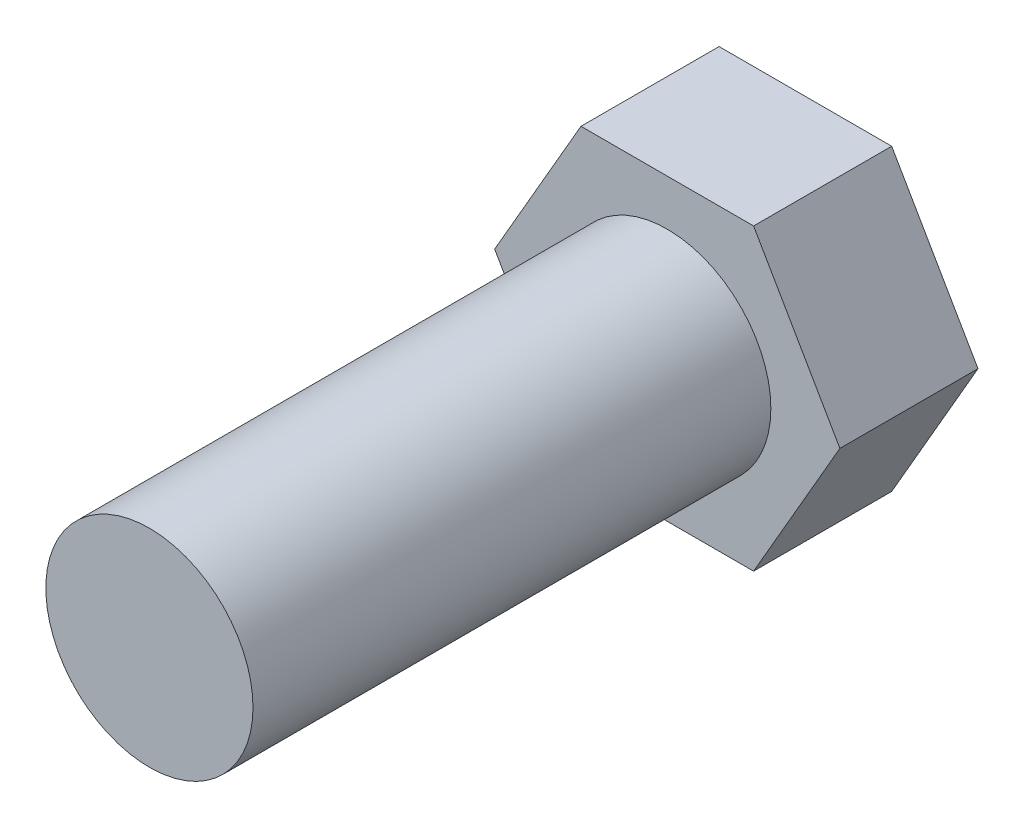
SolidWorks part; units mm, degrees
ref_plane "Alzado" through (0, 0, 0) normal (0, 0, 1) x (1, 0, 0)
ref_plane "Planta" through (0, 0, 0) normal (0, 1, 0) x (1, 0, 0)
ref_plane "Vista lateral" through (0, 0, 0) normal (1, 0, 0) x (0, 0, -1)
sketch "Croquis2" plane through (0, 0, 0) normal (0, 0, 1) x (1, 0, 0)
  circle A0 centre (0, 0) radius 3
extrude "Saliente-Extruir1" add sketch "Croquis2" along normal blind 15
sketch "Croquis3" plane through (0, 0, 0) normal (0, 0, -1) x (-1, 0, 0)
  line L1 (5, 0) -> (2.5, 4.3301)
  line L2 (2.5, 4.3301) -> (-2.5, 4.3301)
  line L3 (-2.5, 4.3301) -> (-5, 0)
  line L4 (-5, 0) -> (-2.5, -4.3301)
  line L5 (-2.5, -4.3301) -> (2.5, -4.3301)
  line L6 (2.5, -4.3301) -> (5, 0)
  circle A1 centre (0, 0) radius 4.3301 construction
  dimension "D1" = 5
extrude "Saliente-Extruir3" add sketch "Croquis3" along normal blind 4
